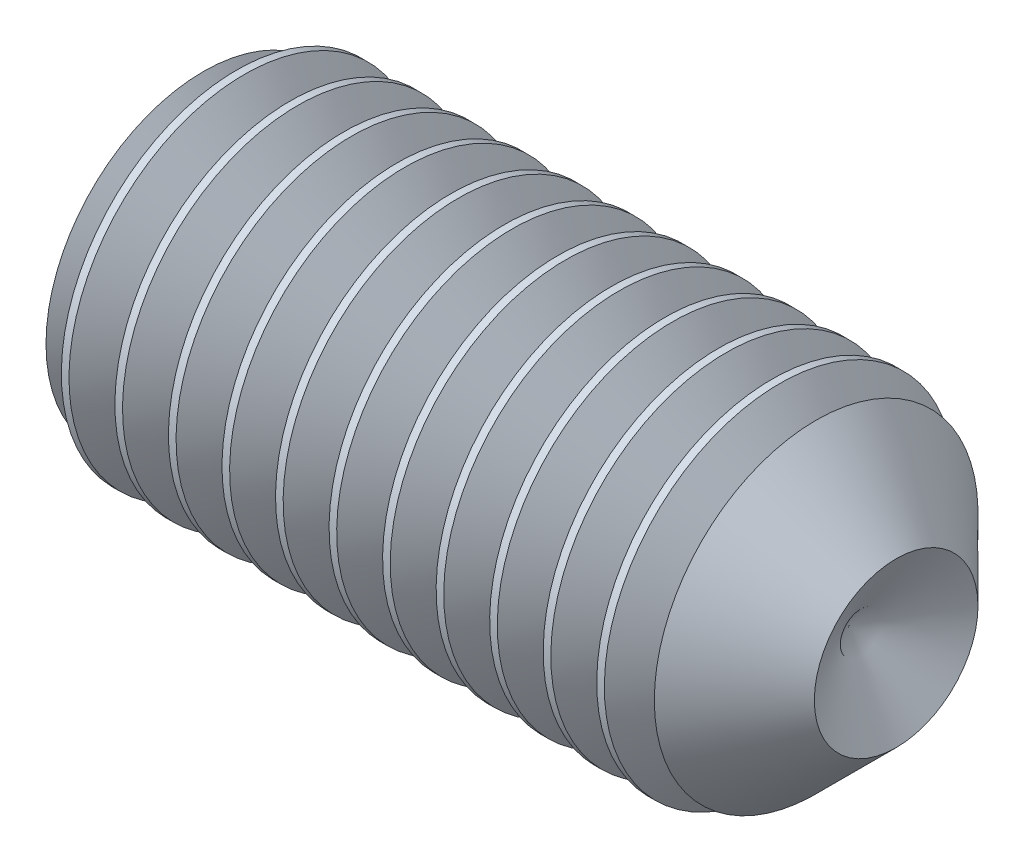
SolidWorks part; units mm, degrees
ref_plane "Plane1" through (0, 0, 0) normal (0, 0, 1) x (1, 0, 0)
ref_plane "Plane2" through (0, 0, 0) normal (0, 1, 0) x (1, 0, 0)
ref_plane "Plane3" through (0, 0, 0) normal (1, 0, 0) x (0, 0, -1)
sketch "BodySke" plane through (0, 0, 0) normal (0, 0, 1) x (1, 0, 0)
  line L0 (0, 0) -> (0, 1.2195)
  line L1 (0, 1.2195) -> (0.1619, 1.5)
  line L2 (0.1619, 1.5) -> (5.2, 1.5)
  line L3 (5.2, 1.5) -> (6, 0.7)
  line L4 (5.5959, 0) -> (0, 0)
  line L5 (-12.7, 0) -> (88.9, 0) construction
  line L6 (5.5959, 0) -> (6, 0.7)
  line L7 (6, 0.7) -> (6, 10.225) construction
  line L8 (0, -1.2195) -> (0.1619, -1.5) construction
  line L9 (5.5959, 0) -> (6, -0.7) construction
  line L10 (5.2, -1.5) -> (6, -0.7) construction
  line L11 (0.25, 15.875) -> (0.25, -3.175) construction
  dimension "Length" = 6
  dimension "Diameter" = 3
  dimension "Drive_ch_ang" = 60
  dimension "Minor_dia" = 2.439
  dimension "Cup_nose_ang" = 45
  dimension "Cup_ang" = 120
  dimension "Cup_dia" = 1.4
  dimension "Advance" = 0.5
revolve "BaseBody" add sketch "BodySke" angle 360 about L5
cosmetic thread "ThreadCosmetic" [suppressed] parameters "Thread_minor"=2.439
sketch "Sketch2" plane through (0, 0, 0) normal (-1, 0, 0) x (0, 0, 1)
  line L0 (0.433, 0.75) -> (-0.433, 0.75)
  line L1 (-0.433, 0.75) -> (-0.866, 0)
  line L2 (0.433, 0.75) -> (0.866, 0)
  line L3 (0.433, -0.75) -> (0.866, 0)
  line L4 (0.433, -0.75) -> (-0.433, -0.75)
  line L5 (-0.433, -0.75) -> (-0.866, 0)
  dimension "Hex_size" = 1.5
  dimension "D2" = 0.75
  dimension "D3" = 0.75
extrude "Hex" cut sketch "Sketch2" against normal blind 2
sketch "ThdSchSke" plane through (0, 0, 0) normal (0, 0, 1) x (1, 0, 0)
  line L0 (0.1619, -1.2195) -> (-0.0345, -1.5)
  line L1 (0.1619, -1.2195) -> (0.3584, -1.5)
  line L2 (0.3584, -1.5) -> (0.3584, -1.875)
  line L3 (-3.175, 0) -> (5.1513, 0) construction
  line L4 (0.1619, 1.5) -> (0.1619, -1.5) construction
  line L5 (0.3584, -1.875) -> (-0.0345, -1.875)
  line L6 (-0.0345, -1.875) -> (-0.0345, -1.5)
  dimension "Thread_minor" = 2.439
  dimension "Diameter" = 3
  dimension "SideAngle" = 55
  dimension "VeeAngle" = 70
  dimension "Overcut" = 3.75
revolve "ThreadSchematic" cut sketch "ThdSchSke" angle 360 about L3
pattern_linear "ThdSchPat" count 12 spacing 0.458 along (1, 0, 0) of "ThreadSchematic"
equation "\"D2@Sketch2\" = \"Hex_size@Sketch2\" / 2"
equation "\"D3@Sketch2\" = \"Hex_size@Sketch2\" / 2"
equation "\"Thread_minor@ThreadCosmetic\" = \"Minor_dia@BodySke\""
equation "\"Thread_minor@ThdSchSke\" = \"Thread_minor@ThreadCosmetic\""
equation "\"Diameter@ThdSchSke\" = \"Diameter@BodySke\""
equation "\"Overcut@ThdSchSke\" = \"Diameter@BodySke\" * 1.25"
equation "\"Num_threads@ThdSchPat\" = int( (\"Length@BodySke\" - ( ( ( \"Diameter@BodySke\" - \"Minor_dia@BodySke\" ) * 0.5 ) / tan( \"Drive_ch_ang@BodySke\" * 0.017453292 ) ) - ( ( ( \"Diameter@BodySke\" - \"Cup_dia@BodySke\" ) * 0.5 ) * tan( \"Cup_nose_ang@BodySke\" * 0.017453292 ) ) ) / \"Advance@BodySke\" + 0.999 )  + 1"
equation "\"Advance@ThdSchPat\" = (\"Length@BodySke\" - ( ( ( \"Diameter@BodySke\" - \"Minor_dia@BodySke\" ) * 0.5 ) / tan( \"Drive_ch_ang@BodySke\" * 0.017453292 ) ) - ( ( ( \"Diameter@BodySke\" - \"Cup_dia@BodySke\" ) * 0.5 ) * tan( \"Cup_nose_ang@BodySke\" * 0.017453292 ) ) ) /  (\"Num_threads@ThdSchPat\" - 1) 'relax it"
equation "' \"Num_threads@ThdSchPat\" = \"Num_threads@ThdSchPat\" - sgn( \"Num_threads@ThdSchPat\" - 1) '---chamfered tips only---"
